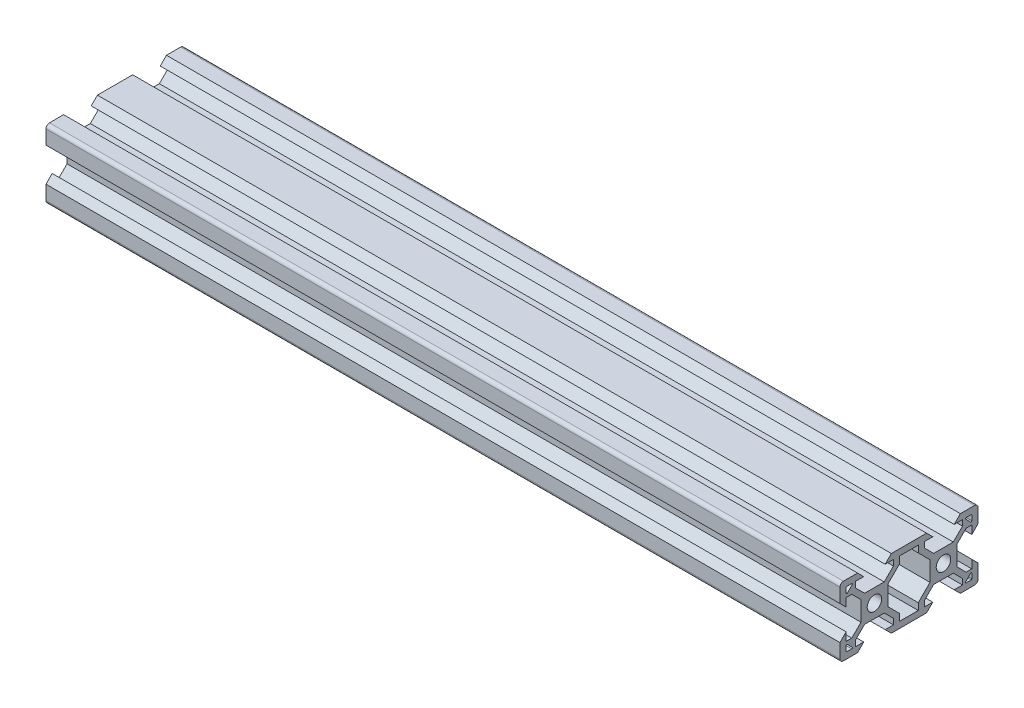
SolidWorks part; units mm, degrees
material "1060 Alloy"
ref_plane "Front Plane" through (0, 0, 0) normal (0, 0, 1) x (1, 0, 0)
ref_plane "Top Plane" through (0, 0, 0) normal (0, 1, 0) x (1, 0, 0)
ref_plane "Right Plane" through (0, 0, 0) normal (1, 0, 0) x (0, 0, -1)
sketch "Sketch4" plane through (0, 0, 0) normal (1, 0, 0) x (0, 0, -1)
  line L0 (-19.2399, 7.0114) -> (20.7601, 7.0114) construction
  dimension "D1" = 40
sketch "Sketch5" plane through (0, 0, 0) normal (1, 0, 0) x (0, 0, -1)
  line L0 (-19.998, 4.9) -> (-18.198, 3.1)
  line L1 (-18.198, 3.1) -> (-18.198, 5.4993)
  line L2 (-18.198, 5.4993) -> (-16.558, 5.4993)
  line L3 (-16.558, 5.4993) -> (-13.9, 2.8413)
  line L4 (-13.9, 2.8413) -> (-13.9, -2.8387)
  line L5 (-13.9, -2.8387) -> (-16.558, -5.4967)
  line L6 (-16.558, -5.4967) -> (-18.198, -5.4967)
  line L7 (-18.198, -5.4967) -> (-18.198, -3.1)
  line L8 (-18.198, -3.1) -> (-19.998, -4.9)
  line L9 (-19.998, -4.9) -> (-19.998, -9)
  line L10 (-18.998, -10) -> (-14.9, -10)
  line L11 (-14.9, -10) -> (-13.1, -8.2)
  line L12 (-13.1, -8.2) -> (-15.5, -8.2)
  line L13 (-15.5, -8.2) -> (-15.5, -6.56)
  line L14 (-15.5, -6.56) -> (-12.84, -3.9)
  line L15 (-12.84, -3.9) -> (-7.16, -3.9)
  line L16 (-7.16, -3.9) -> (-4.5, -6.56)
  line L17 (-4.5, -6.56) -> (-4.5, -8.2)
  line L18 (-4.5, -8.2) -> (-6.9, -8.2)
  line L19 (-6.9, -8.2) -> (-5.1, -10)
  line L20 (-5.1, -10) -> (5.1, -10)
  line L21 (5.1, -10) -> (6.9, -8.2)
  line L22 (6.9, -8.2) -> (4.496, -8.2)
  line L23 (4.496, -8.2) -> (4.496, -6.56)
  line L24 (4.496, -6.56) -> (7.156, -3.9)
  line L25 (7.156, -3.9) -> (12.836, -3.9)
  line L26 (12.836, -3.9) -> (15.496, -6.56)
  line L27 (15.496, -6.56) -> (15.496, -8.2)
  line L28 (15.496, -8.2) -> (13.1, -8.2)
  line L29 (13.1, -8.2) -> (14.9, -10)
  line L30 (14.9, -10) -> (19.002, -10)
  line L31 (20.002, -9) -> (20.002, -4.9)
  line L32 (20.002, -4.9) -> (18.202, -3.1)
  line L33 (18.202, -3.1) -> (18.202, -5.5046)
  line L34 (18.202, -5.5046) -> (16.562, -5.5046)
  line L35 (16.562, -5.5046) -> (13.9, -2.8426)
  line L36 (13.9, -2.8426) -> (13.9, 2.8374)
  line L37 (13.9, 2.8374) -> (16.562, 5.4993)
  line L38 (16.562, 5.4993) -> (18.202, 5.4993)
  line L39 (18.202, 5.4993) -> (18.202, 3.1)
  line L40 (18.202, 3.1) -> (20.002, 4.9)
  line L41 (20.002, 4.9) -> (20.002, 9)
  line L42 (19.002, 10) -> (14.9, 10)
  line L43 (14.9, 10) -> (13.1, 8.2)
  line L44 (13.1, 8.2) -> (15.5013, 8.2)
  line L45 (15.5013, 8.2) -> (15.5013, 6.56)
  line L46 (15.5013, 6.56) -> (12.8413, 3.9)
  line L47 (12.8413, 3.9) -> (7.1613, 3.9)
  line L48 (7.1613, 3.9) -> (4.5013, 6.56)
  line L49 (4.5013, 6.56) -> (4.5013, 8.2)
  line L50 (4.5013, 8.2) -> (6.9, 8.2)
  line L51 (6.9, 8.2) -> (5.1, 10)
  line L52 (5.1, 10) -> (-5.1, 10)
  line L53 (-5.1, 10) -> (-6.9, 8.2)
  line L54 (-6.9, 8.2) -> (-4.5013, 8.2)
  line L55 (-4.5013, 8.2) -> (-4.5013, 6.56)
  line L56 (-4.5013, 6.56) -> (-7.1613, 3.9)
  line L57 (-7.1613, 3.9) -> (-12.8413, 3.9)
  line L58 (-12.8413, 3.9) -> (-15.5013, 6.56)
  line L59 (-15.5013, 6.56) -> (-15.5013, 8.2)
  line L60 (-15.5013, 8.2) -> (-13.1, 8.2)
  line L61 (-13.1, 8.2) -> (-14.9, 10)
  line L62 (-14.9, 10) -> (-18.998, 10)
  line L63 (-19.998, 9) -> (-19.998, 4.9)
  line L64 (6.1, -2.84) -> (6.1, 2.84)
  line L65 (6.1, 2.84) -> (2.7, 6.24)
  line L66 (2.7, 6.24) -> (2.7, 8.2)
  line L67 (2.7, 8.2) -> (-2.7, 8.2)
  line L68 (-2.7, 8.2) -> (-2.7, 6.24)
  line L69 (-2.7, 6.24) -> (-6.1, 2.84)
  line L70 (-6.1, 2.84) -> (-6.1, -2.84)
  line L71 (-6.1, -2.84) -> (-2.7, -6.24)
  line L72 (-2.7, -6.24) -> (-2.7, -8.2)
  line L73 (-2.7, -8.2) -> (2.7, -8.2)
  line L74 (2.7, -8.2) -> (2.7, -6.24)
  line L75 (2.7, -6.24) -> (6.1, -2.84)
  line L76 (0, -8.2) -> (0, 8.2) construction
  line L77 (6.1, 0) -> (-6.1, 0) construction
  line L78 (16.562, 5.4993) -> (15.5013, 6.56) construction
  line L79 (16.5713, 8.2) -> (18.002, 8.2)
  line L81 (17.8606, 6.4279) -> (16.4299, 7.8586)
  line L82 (18.202, 8) -> (18.202, 6.5693)
  line L83 (18.002, 6.5693) -> (18.002, 8) construction
  line L84 (18.002, 8) -> (16.5713, 8) construction
  line L85 (16.5713, 8) -> (18.002, 6.5693) construction
  line L86 (16.5713, -8.2) -> (18.002, -8.2)
  line L87 (18.202, -8) -> (18.202, -6.5693)
  line L88 (17.8606, -6.4279) -> (16.4299, -7.8586)
  line L89 (-17.8606, 6.4279) -> (-16.4299, 7.8586)
  line L90 (-16.5713, 8.2) -> (-18.002, 8.2)
  line L91 (-18.202, 8) -> (-18.202, 6.5693)
  line L92 (-16.5713, -8.2) -> (-18.002, -8.2)
  line L93 (-17.8606, -6.4279) -> (-16.4299, -7.8586)
  line L94 (-18.202, -8) -> (-18.202, -6.5693)
  circle A0 centre (-10, 0) radius 2.1
  circle A1 centre (10, 0) radius 2.1
  arc A2 (-19.998, -9) -> (-18.998, -10) centre (-18.998, -9) ccw
  arc A5 (-18.998, 10) -> (-19.998, 9) centre (-18.998, 9) ccw
  arc A6 (20.002, -9) -> (19.002, -10) centre (19.002, -9) cw
  arc A7 (20.002, 9) -> (19.002, 10) centre (19.002, 9) ccw
  arc A8 (18.002, 8.2) -> (18.202, 8) centre (18.002, 8) cw
  arc A10 (16.4299, 7.8586) -> (16.5713, 8.2) centre (16.5713, 8) cw
  arc A12 (18.202, 6.5693) -> (17.8606, 6.4279) centre (18.002, 6.5693) cw
  arc A13 (16.4299, -7.8586) -> (16.5713, -8.2) centre (16.5713, -8) ccw
  arc A14 (18.002, -8.2) -> (18.202, -8) centre (18.002, -8) ccw
  arc A15 (18.202, -6.5693) -> (17.8606, -6.4279) centre (18.002, -6.5693) ccw
  arc A16 (-18.202, 6.5693) -> (-17.8606, 6.4279) centre (-18.002, 6.5693) ccw
  arc A17 (-16.4299, 7.8586) -> (-16.5713, 8.2) centre (-16.5713, 8) ccw
  arc A18 (-18.002, 8.2) -> (-18.202, 8) centre (-18.002, 8) ccw
  arc A19 (-18.002, -8.2) -> (-18.202, -8) centre (-18.002, -8) cw
  arc A20 (-16.4299, -7.8586) -> (-16.5713, -8.2) centre (-16.5713, -8) cw
  arc A21 (-18.202, -6.5693) -> (-17.8606, -6.4279) centre (-18.002, -6.5693) cw
  dimension "D1" = 4.2
  dimension "D20" = 3.9
  dimension "D27" = 1
  dimension "D40" = 1
  dimension "D41" = 1
  dimension "D42" = 1
  dimension "D45" = 0.2
  dimension "D47" = 1.07
  dimension "D48" = 1.07
  dimension "D49" = 0.2
  dimension "D2" = 20
  dimension "D3" = 10
  dimension "D4" = 5.68
  dimension "D5" = 5.4
  dimension "D6" = 1.96
  dimension "D7" = 45
  dimension "D8" = 1.8
  dimension "D9" = 1.64
  dimension "D10" = 1.8
  dimension "D11" = 40
  dimension "D12" = 20
  dimension "D13" = 3.9
  dimension "D14" = 1.5
  dimension "D15" = 1.5
  dimension "D16" = 3.9
  dimension "D17" = 3.9
  dimension "D18" = 3.9
  dimension "D19" = 3.9
  dimension "D21" = 1.5
  dimension "D22" = 1.5
  dimension "D23" = 1.64
  dimension "D24" = 45
  dimension "D25" = 1.5
  dimension "D26" = 1.8
  dimension "D28" = 6.2
  dimension "D29" = 6.2
  dimension "D30" = 6.2
  dimension "D31" = 6.2
  dimension "D32" = 6.2
  dimension "D33" = 3.1
  dimension "D34" = 3.1
  dimension "D35" = 3.1
  dimension "D36" = 3.1
  dimension "D37" = 6.2
  dimension "D38" = 3.1
  dimension "D39" = 3.1
  dimension "D43" = 1.64
  dimension "D44" = 135
  dimension "D46" = 45
extrude "Boss-Extrude1" add sketch "Sketch5" along normal mid plane 230
